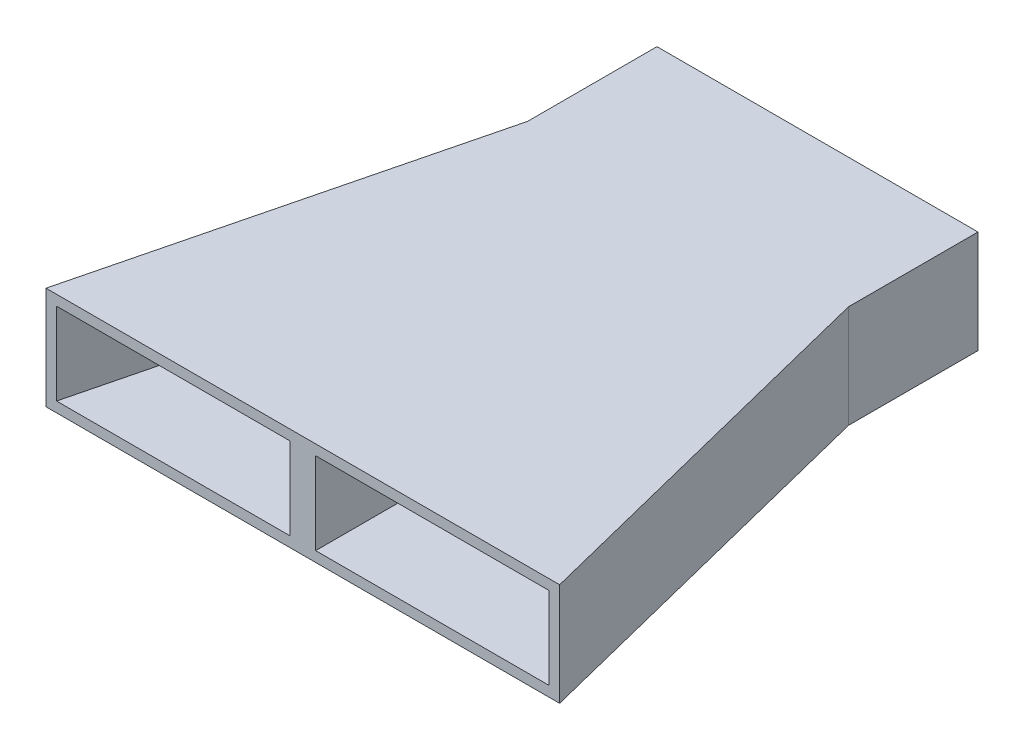
SolidWorks part; units mm, degrees
material "POM Acetal Copolymer"
ref_plane "Front Plane" through (0, 0, 0) normal (0, 0, 1) x (1, 0, 0)
ref_plane "Top Plane" through (0, 0, 0) normal (0, 1, 0) x (1, 0, 0)
ref_plane "Right Plane" through (0, 0, 0) normal (1, 0, 0) x (0, 0, -1)
sketch "Sketch1" plane through (0, 0, 0) normal (0, 1, 0) x (1, 0, 0)
  line L0 (0, 0) -> (0, 74.7716) construction
  line L1 (12.7, 0) -> (-12.7, 0)
  line L2 (-12.7, 0) -> (-7.9375, 19.05)
  line L3 (-7.9375, 19.05) -> (7.9375, 19.05) construction
  line L4 (12.7, 0) -> (7.9375, 19.05)
  line L5 (-7.9375, 19.05) -> (-7.9375, 25.4508)
  line L6 (-7.9375, 25.4508) -> (7.9375, 25.4508)
  line L7 (7.9375, 25.4508) -> (7.9375, 19.05)
  point P7 (0, 19.05)
  dimension "D1" = 15.875
  dimension "D2" = 25.4
  dimension "D3" = 19.05
  dimension "D4" = 6.4008
extrude "Extrude1" add sketch "Sketch1" along normal blind 5.08
shell "Shell1" thickness 0.508
sketch "Sketch2" plane through (0, 0.508, 0) normal (0, 1, 0) x (-1, 0, 0)
  line L0 (0, -25.4508) -> (0, 0) construction
  line L2 (0.635, -25.4508) -> (0.635, 0)
  line L3 (-0.635, -25.4508) -> (-0.635, 0)
  line L4 (0.635, -25.4508) -> (-0.635, -25.4508)
  line L5 (0.635, 0) -> (-0.635, 0)
  line L6 (0, -25.4508) -> (0, 0) construction
  line L7 (-7.9375, -25.4508) -> (7.9375, -25.4508) construction
  dimension "D1" = 0.635
  dimension "D2" = 0.635
extrude "Extrude2" add sketch "Sketch2" along normal up to next
